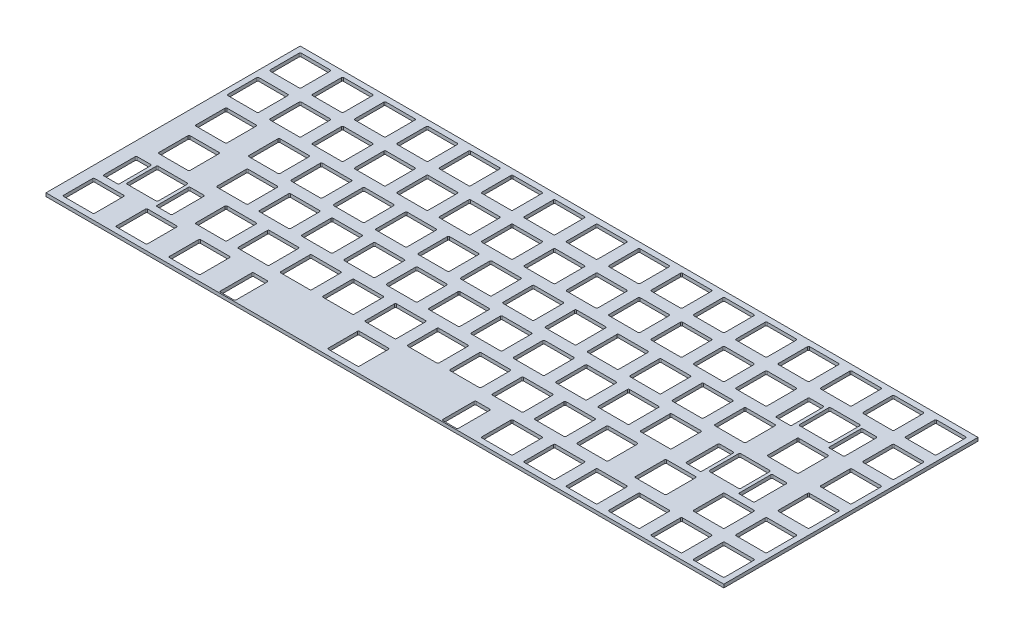
SolidWorks part; units mm, degrees
ref_plane "Front Plane" through (0, 0, 0) normal (0, 0, 1) x (1, 0, 0)
ref_plane "Top Plane" through (0, 0, 0) normal (0, 1, 0) x (1, 0, 0)
ref_plane "Right Plane" through (0, 0, 0) normal (1, 0, 0) x (0, 0, -1)
sketch "Sketch2" plane through (0, 0, 0) normal (0, 1, 0) x (1, 0, 0)
  line L0 (3.025, -2.525) -> (16.025, -2.525)
  line L1 (3.025, -16.525) -> (16.025, -16.525)
  line L2 (2.525, -3.025) -> (2.525, -16.025)
  line L3 (16.525, -3.025) -> (16.525, -16.025)
  line L4 (22.075, -2.525) -> (35.075, -2.525)
  line L5 (22.075, -16.525) -> (35.075, -16.525)
  line L6 (21.575, -3.025) -> (21.575, -16.025)
  line L7 (35.575, -3.025) -> (35.575, -16.025)
  line L8 (41.125, -2.525) -> (54.125, -2.525)
  line L9 (41.125, -16.525) -> (54.125, -16.525)
  line L10 (40.625, -3.025) -> (40.625, -16.025)
  line L11 (54.625, -3.025) -> (54.625, -16.025)
  line L12 (60.175, -2.525) -> (73.175, -2.525)
  line L13 (60.175, -16.525) -> (73.175, -16.525)
  line L14 (59.675, -3.025) -> (59.675, -16.025)
  line L15 (73.675, -3.025) -> (73.675, -16.025)
  line L16 (79.225, -2.525) -> (92.225, -2.525)
  line L17 (79.225, -16.525) -> (92.225, -16.525)
  line L18 (78.725, -3.025) -> (78.725, -16.025)
  line L19 (92.725, -3.025) -> (92.725, -16.025)
  line L20 (98.275, -2.525) -> (111.275, -2.525)
  line L21 (98.275, -16.525) -> (111.275, -16.525)
  line L22 (97.775, -3.025) -> (97.775, -16.025)
  line L23 (111.775, -3.025) -> (111.775, -16.025)
  line L24 (117.325, -2.525) -> (130.325, -2.525)
  line L25 (117.325, -16.525) -> (130.325, -16.525)
  line L26 (116.825, -3.025) -> (116.825, -16.025)
  line L27 (130.825, -3.025) -> (130.825, -16.025)
  line L28 (136.375, -2.525) -> (149.375, -2.525)
  line L29 (136.375, -16.525) -> (149.375, -16.525)
  line L30 (135.875, -3.025) -> (135.875, -16.025)
  line L31 (149.875, -3.025) -> (149.875, -16.025)
  line L32 (155.425, -2.525) -> (168.425, -2.525)
  line L33 (155.425, -16.525) -> (168.425, -16.525)
  line L34 (154.925, -3.025) -> (154.925, -16.025)
  line L35 (168.925, -3.025) -> (168.925, -16.025)
  line L36 (174.475, -2.525) -> (187.475, -2.525)
  line L37 (174.475, -16.525) -> (187.475, -16.525)
  line L38 (173.975, -3.025) -> (173.975, -16.025)
  line L39 (187.975, -3.025) -> (187.975, -16.025)
  line L40 (193.525, -2.525) -> (206.525, -2.525)
  line L41 (193.525, -16.525) -> (206.525, -16.525)
  line L42 (193.025, -3.025) -> (193.025, -16.025)
  line L43 (207.025, -3.025) -> (207.025, -16.025)
  line L44 (212.575, -2.525) -> (225.575, -2.525)
  line L45 (212.575, -16.525) -> (225.575, -16.525)
  line L46 (212.075, -3.025) -> (212.075, -16.025)
  line L47 (226.075, -3.025) -> (226.075, -16.025)
  line L48 (231.625, -2.525) -> (244.625, -2.525)
  line L49 (231.625, -16.525) -> (244.625, -16.525)
  line L50 (231.125, -3.025) -> (231.125, -16.025)
  line L51 (245.125, -3.025) -> (245.125, -16.025)
  line L52 (250.675, -2.525) -> (263.675, -2.525)
  line L53 (250.675, -16.525) -> (263.675, -16.525)
  line L54 (250.175, -3.025) -> (250.175, -16.025)
  line L55 (264.175, -3.025) -> (264.175, -16.025)
  line L56 (269.725, -2.525) -> (282.725, -2.525)
  line L57 (269.725, -16.525) -> (282.725, -16.525)
  line L58 (269.225, -3.025) -> (269.225, -16.025)
  line L59 (283.225, -3.025) -> (283.225, -16.025)
  line L60 (288.775, -2.525) -> (301.775, -2.525)
  line L61 (288.775, -16.525) -> (301.775, -16.525)
  line L62 (288.275, -3.025) -> (288.275, -16.025)
  line L63 (302.275, -3.025) -> (302.275, -16.025)
  line L64 (3.025, -21.575) -> (16.025, -21.575)
  line L65 (3.025, -35.575) -> (16.025, -35.575)
  line L66 (2.525, -22.075) -> (2.525, -35.075)
  line L67 (16.525, -22.075) -> (16.525, -35.075)
  line L68 (22.075, -21.575) -> (35.075, -21.575)
  line L69 (22.075, -35.575) -> (35.075, -35.575)
  line L70 (21.575, -22.075) -> (21.575, -35.075)
  line L71 (35.575, -22.075) -> (35.575, -35.075)
  line L72 (41.125, -21.575) -> (54.125, -21.575)
  line L73 (41.125, -35.575) -> (54.125, -35.575)
  line L74 (40.625, -22.075) -> (40.625, -35.075)
  line L75 (54.625, -22.075) -> (54.625, -35.075)
  line L76 (60.175, -21.575) -> (73.175, -21.575)
  line L77 (60.175, -35.575) -> (73.175, -35.575)
  line L78 (59.675, -22.075) -> (59.675, -35.075)
  line L79 (73.675, -22.075) -> (73.675, -35.075)
  line L80 (79.225, -21.575) -> (92.225, -21.575)
  line L81 (79.225, -35.575) -> (92.225, -35.575)
  line L82 (78.725, -22.075) -> (78.725, -35.075)
  line L83 (92.725, -22.075) -> (92.725, -35.075)
  line L84 (98.275, -21.575) -> (111.275, -21.575)
  line L85 (98.275, -35.575) -> (111.275, -35.575)
  line L86 (97.775, -22.075) -> (97.775, -35.075)
  line L87 (111.775, -22.075) -> (111.775, -35.075)
  line L88 (117.325, -21.575) -> (130.325, -21.575)
  line L89 (117.325, -35.575) -> (130.325, -35.575)
  line L90 (116.825, -22.075) -> (116.825, -35.075)
  line L91 (130.825, -22.075) -> (130.825, -35.075)
  line L92 (136.375, -21.575) -> (149.375, -21.575)
  line L93 (136.375, -35.575) -> (149.375, -35.575)
  line L94 (135.875, -22.075) -> (135.875, -35.075)
  line L95 (149.875, -22.075) -> (149.875, -35.075)
  line L96 (155.425, -21.575) -> (168.425, -21.575)
  line L97 (155.425, -35.575) -> (168.425, -35.575)
  line L98 (154.925, -22.075) -> (154.925, -35.075)
  line L99 (168.925, -22.075) -> (168.925, -35.075)
  line L100 (174.475, -21.575) -> (187.475, -21.575)
  line L101 (174.475, -35.575) -> (187.475, -35.575)
  line L102 (173.975, -22.075) -> (173.975, -35.075)
  line L103 (187.975, -22.075) -> (187.975, -35.075)
  line L104 (193.525, -21.575) -> (206.525, -21.575)
  line L105 (193.525, -35.575) -> (206.525, -35.575)
  line L106 (193.025, -22.075) -> (193.025, -35.075)
  line L107 (207.025, -22.075) -> (207.025, -35.075)
  line L108 (212.575, -21.575) -> (225.575, -21.575)
  line L109 (212.575, -35.575) -> (225.575, -35.575)
  line L110 (212.075, -22.075) -> (212.075, -35.075)
  line L111 (226.075, -22.075) -> (226.075, -35.075)
  line L112 (231.625, -21.575) -> (244.625, -21.575)
  line L113 (231.625, -35.575) -> (244.625, -35.575)
  line L114 (231.125, -22.075) -> (231.125, -35.075)
  line L115 (245.125, -22.075) -> (245.125, -35.075)
  line L116 (260.2, -21.575) -> (273.2, -21.575)
  line L117 (260.2, -35.575) -> (273.2, -35.575)
  line L118 (259.7, -22.075) -> (259.7, -35.075)
  line L119 (273.7, -22.075) -> (273.7, -35.075)
  line L120 (251.762, -22.575) -> (257.762, -22.575)
  line L121 (251.762, -37.575) -> (257.762, -37.575)
  line L122 (251.262, -23.075) -> (251.262, -37.075)
  line L123 (258.262, -23.075) -> (258.262, -37.075)
  line L124 (275.638, -22.575) -> (281.638, -22.575)
  line L125 (275.638, -37.575) -> (281.638, -37.575)
  line L126 (275.138, -23.075) -> (275.138, -37.075)
  line L127 (282.138, -23.075) -> (282.138, -37.075)
  line L128 (288.775, -21.575) -> (301.775, -21.575)
  line L129 (288.775, -35.575) -> (301.775, -35.575)
  line L130 (288.275, -22.075) -> (288.275, -35.075)
  line L131 (302.275, -22.075) -> (302.275, -35.075)
  line L132 (7.7875, -40.625) -> (20.7875, -40.625)
  line L133 (7.7875, -54.625) -> (20.7875, -54.625)
  line L134 (7.2875, -41.125) -> (7.2875, -54.125)
  line L135 (21.2875, -41.125) -> (21.2875, -54.125)
  line L136 (31.6, -40.625) -> (44.6, -40.625)
  line L137 (31.6, -54.625) -> (44.6, -54.625)
  line L138 (31.1, -41.125) -> (31.1, -54.125)
  line L139 (45.1, -41.125) -> (45.1, -54.125)
  line L140 (50.65, -40.625) -> (63.65, -40.625)
  line L141 (50.65, -54.625) -> (63.65, -54.625)
  line L142 (50.15, -41.125) -> (50.15, -54.125)
  line L143 (64.15, -41.125) -> (64.15, -54.125)
  line L144 (69.7, -40.625) -> (82.7, -40.625)
  line L145 (69.7, -54.625) -> (82.7, -54.625)
  line L146 (69.2, -41.125) -> (69.2, -54.125)
  line L147 (83.2, -41.125) -> (83.2, -54.125)
  line L148 (88.75, -40.625) -> (101.75, -40.625)
  line L149 (88.75, -54.625) -> (101.75, -54.625)
  line L150 (88.25, -41.125) -> (88.25, -54.125)
  line L151 (102.25, -41.125) -> (102.25, -54.125)
  line L152 (107.8, -40.625) -> (120.8, -40.625)
  line L153 (107.8, -54.625) -> (120.8, -54.625)
  line L154 (107.3, -41.125) -> (107.3, -54.125)
  line L155 (121.3, -41.125) -> (121.3, -54.125)
  line L156 (126.85, -40.625) -> (139.85, -40.625)
  line L157 (126.85, -54.625) -> (139.85, -54.625)
  line L158 (126.35, -41.125) -> (126.35, -54.125)
  line L159 (140.35, -41.125) -> (140.35, -54.125)
  line L160 (145.9, -40.625) -> (158.9, -40.625)
  line L161 (145.9, -54.625) -> (158.9, -54.625)
  line L162 (145.4, -41.125) -> (145.4, -54.125)
  line L163 (159.4, -41.125) -> (159.4, -54.125)
  line L164 (164.95, -40.625) -> (177.95, -40.625)
  line L165 (164.95, -54.625) -> (177.95, -54.625)
  line L166 (164.45, -41.125) -> (164.45, -54.125)
  line L167 (178.45, -41.125) -> (178.45, -54.125)
  line L168 (184, -40.625) -> (197, -40.625)
  line L169 (184, -54.625) -> (197, -54.625)
  line L170 (183.5, -41.125) -> (183.5, -54.125)
  line L171 (197.5, -41.125) -> (197.5, -54.125)
  line L172 (203.05, -40.625) -> (216.05, -40.625)
  line L173 (203.05, -54.625) -> (216.05, -54.625)
  line L174 (202.55, -41.125) -> (202.55, -54.125)
  line L175 (216.55, -41.125) -> (216.55, -54.125)
  line L176 (222.1, -40.625) -> (235.1, -40.625)
  line L177 (222.1, -54.625) -> (235.1, -54.625)
  line L178 (221.6, -41.125) -> (221.6, -54.125)
  line L179 (235.6, -41.125) -> (235.6, -54.125)
  line L180 (241.15, -40.625) -> (254.15, -40.625)
  line L181 (241.15, -54.625) -> (254.15, -54.625)
  line L182 (240.65, -41.125) -> (240.65, -54.125)
  line L183 (254.65, -41.125) -> (254.65, -54.125)
  line L184 (264.9625, -40.625) -> (277.9625, -40.625)
  line L185 (264.9625, -54.625) -> (277.9625, -54.625)
  line L186 (264.4625, -41.125) -> (264.4625, -54.125)
  line L187 (278.4625, -41.125) -> (278.4625, -54.125)
  line L188 (288.775, -40.625) -> (301.775, -40.625)
  line L189 (288.775, -54.625) -> (301.775, -54.625)
  line L190 (288.275, -41.125) -> (288.275, -54.125)
  line L191 (302.275, -41.125) -> (302.275, -54.125)
  line L192 (10.1687, -59.675) -> (23.1687, -59.675)
  line L193 (10.1687, -73.675) -> (23.1687, -73.675)
  line L194 (9.6688, -60.175) -> (9.6688, -73.175)
  line L195 (23.6687, -60.175) -> (23.6687, -73.175)
  line L196 (36.3625, -59.675) -> (49.3625, -59.675)
  line L197 (36.3625, -73.675) -> (49.3625, -73.675)
  line L198 (35.8625, -60.175) -> (35.8625, -73.175)
  line L199 (49.8625, -60.175) -> (49.8625, -73.175)
  line L200 (55.4125, -59.675) -> (68.4125, -59.675)
  line L201 (55.4125, -73.675) -> (68.4125, -73.675)
  line L202 (54.9125, -60.175) -> (54.9125, -73.175)
  line L203 (68.9125, -60.175) -> (68.9125, -73.175)
  line L204 (74.4625, -59.675) -> (87.4625, -59.675)
  line L205 (74.4625, -73.675) -> (87.4625, -73.675)
  line L206 (73.9625, -60.175) -> (73.9625, -73.175)
  line L207 (87.9625, -60.175) -> (87.9625, -73.175)
  line L208 (93.5125, -59.675) -> (106.5125, -59.675)
  line L209 (93.5125, -73.675) -> (106.5125, -73.675)
  line L210 (93.0125, -60.175) -> (93.0125, -73.175)
  line L211 (107.0125, -60.175) -> (107.0125, -73.175)
  line L212 (112.5625, -59.675) -> (125.5625, -59.675)
  line L213 (112.5625, -73.675) -> (125.5625, -73.675)
  line L214 (112.0625, -60.175) -> (112.0625, -73.175)
  line L215 (126.0625, -60.175) -> (126.0625, -73.175)
  line L216 (131.6125, -59.675) -> (144.6125, -59.675)
  line L217 (131.6125, -73.675) -> (144.6125, -73.675)
  line L218 (131.1125, -60.175) -> (131.1125, -73.175)
  line L219 (145.1125, -60.175) -> (145.1125, -73.175)
  line L220 (150.6625, -59.675) -> (163.6625, -59.675)
  line L221 (150.6625, -73.675) -> (163.6625, -73.675)
  line L222 (150.1625, -60.175) -> (150.1625, -73.175)
  line L223 (164.1625, -60.175) -> (164.1625, -73.175)
  line L224 (169.7125, -59.675) -> (182.7125, -59.675)
  line L225 (169.7125, -73.675) -> (182.7125, -73.675)
  line L226 (169.2125, -60.175) -> (169.2125, -73.175)
  line L227 (183.2125, -60.175) -> (183.2125, -73.175)
  line L228 (188.7625, -59.675) -> (201.7625, -59.675)
  line L229 (188.7625, -73.675) -> (201.7625, -73.675)
  line L230 (188.2625, -60.175) -> (188.2625, -73.175)
  line L231 (202.2625, -60.175) -> (202.2625, -73.175)
  line L232 (207.8125, -59.675) -> (220.8125, -59.675)
  line L233 (207.8125, -73.675) -> (220.8125, -73.675)
  line L234 (207.3125, -60.175) -> (207.3125, -73.175)
  line L235 (221.3125, -60.175) -> (221.3125, -73.175)
  line L236 (226.8625, -59.675) -> (239.8625, -59.675)
  line L237 (226.8625, -73.675) -> (239.8625, -73.675)
  line L238 (226.3625, -60.175) -> (226.3625, -73.175)
  line L239 (240.3625, -60.175) -> (240.3625, -73.175)
  line L240 (257.8188, -59.675) -> (270.8188, -59.675)
  line L241 (257.8188, -73.675) -> (270.8188, -73.675)
  line L242 (257.3188, -60.175) -> (257.3188, -73.175)
  line L243 (271.3188, -60.175) -> (271.3188, -73.175)
  line L244 (249.3808, -60.675) -> (255.3807, -60.675)
  line L245 (249.3808, -75.675) -> (255.3807, -75.675)
  line L246 (248.8808, -61.175) -> (248.8808, -75.175)
  line L247 (255.8807, -61.175) -> (255.8807, -75.175)
  line L248 (273.2568, -60.675) -> (279.2568, -60.675)
  line L249 (273.2568, -75.675) -> (279.2568, -75.675)
  line L250 (272.7568, -61.175) -> (272.7568, -75.175)
  line L251 (279.7568, -61.175) -> (279.7568, -75.175)
  line L252 (288.775, -59.675) -> (301.775, -59.675)
  line L253 (288.775, -73.675) -> (301.775, -73.675)
  line L254 (288.275, -60.175) -> (288.275, -73.175)
  line L255 (302.275, -60.175) -> (302.275, -73.175)
  line L256 (14.9313, -78.725) -> (27.9312, -78.725)
  line L257 (14.9313, -92.725) -> (27.9312, -92.725)
  line L258 (14.4313, -79.225) -> (14.4313, -92.225)
  line L259 (28.4312, -79.225) -> (28.4312, -92.225)
  line L260 (6.4932, -79.725) -> (12.4932, -79.725)
  line L261 (6.4932, -94.725) -> (12.4932, -94.725)
  line L262 (5.9932, -80.225) -> (5.9932, -94.225)
  line L263 (12.9932, -80.225) -> (12.9932, -94.225)
  line L264 (30.3693, -79.725) -> (36.3693, -79.725)
  line L265 (30.3693, -94.725) -> (36.3693, -94.725)
  line L266 (29.8693, -80.225) -> (29.8693, -94.225)
  line L267 (36.8693, -80.225) -> (36.8693, -94.225)
  line L268 (45.8875, -78.725) -> (58.8875, -78.725)
  line L269 (45.8875, -92.725) -> (58.8875, -92.725)
  line L270 (45.3875, -79.225) -> (45.3875, -92.225)
  line L271 (59.3875, -79.225) -> (59.3875, -92.225)
  line L272 (64.9375, -78.725) -> (77.9375, -78.725)
  line L273 (64.9375, -92.725) -> (77.9375, -92.725)
  line L274 (64.4375, -79.225) -> (64.4375, -92.225)
  line L275 (78.4375, -79.225) -> (78.4375, -92.225)
  line L276 (83.9875, -78.725) -> (96.9875, -78.725)
  line L277 (83.9875, -92.725) -> (96.9875, -92.725)
  line L278 (83.4875, -79.225) -> (83.4875, -92.225)
  line L279 (97.4875, -79.225) -> (97.4875, -92.225)
  line L280 (103.0375, -78.725) -> (116.0375, -78.725)
  line L281 (103.0375, -92.725) -> (116.0375, -92.725)
  line L282 (102.5375, -79.225) -> (102.5375, -92.225)
  line L283 (116.5375, -79.225) -> (116.5375, -92.225)
  line L284 (122.0875, -78.725) -> (135.0875, -78.725)
  line L285 (122.0875, -92.725) -> (135.0875, -92.725)
  line L286 (121.5875, -79.225) -> (121.5875, -92.225)
  line L287 (135.5875, -79.225) -> (135.5875, -92.225)
  line L288 (141.1375, -78.725) -> (154.1375, -78.725)
  line L289 (141.1375, -92.725) -> (154.1375, -92.725)
  line L290 (140.6375, -79.225) -> (140.6375, -92.225)
  line L291 (154.6375, -79.225) -> (154.6375, -92.225)
  line L292 (160.1875, -78.725) -> (173.1875, -78.725)
  line L293 (160.1875, -92.725) -> (173.1875, -92.725)
  line L294 (159.6875, -79.225) -> (159.6875, -92.225)
  line L295 (173.6875, -79.225) -> (173.6875, -92.225)
  line L296 (179.2375, -78.725) -> (192.2375, -78.725)
  line L297 (179.2375, -92.725) -> (192.2375, -92.725)
  line L298 (178.7375, -79.225) -> (178.7375, -92.225)
  line L299 (192.7375, -79.225) -> (192.7375, -92.225)
  line L300 (198.2875, -78.725) -> (211.2875, -78.725)
  line L301 (198.2875, -92.725) -> (211.2875, -92.725)
  line L302 (197.7875, -79.225) -> (197.7875, -92.225)
  line L303 (211.7875, -79.225) -> (211.7875, -92.225)
  line L304 (217.3375, -78.725) -> (230.3375, -78.725)
  line L305 (217.3375, -92.725) -> (230.3375, -92.725)
  line L306 (216.8375, -79.225) -> (216.8375, -92.225)
  line L307 (230.8375, -79.225) -> (230.8375, -92.225)
  line L308 (243.5312, -78.725) -> (256.5312, -78.725)
  line L309 (243.5312, -92.725) -> (256.5312, -92.725)
  line L310 (243.0312, -79.225) -> (243.0312, -92.225)
  line L311 (257.0312, -79.225) -> (257.0312, -92.225)
  line L312 (269.725, -78.725) -> (282.725, -78.725)
  line L313 (269.725, -92.725) -> (282.725, -92.725)
  line L314 (269.225, -79.225) -> (269.225, -92.225)
  line L315 (283.225, -79.225) -> (283.225, -92.225)
  line L316 (288.775, -78.725) -> (301.775, -78.725)
  line L317 (288.775, -92.725) -> (301.775, -92.725)
  line L318 (288.275, -79.225) -> (288.275, -92.225)
  line L319 (302.275, -79.225) -> (302.275, -92.225)
  line L320 (5.4063, -97.775) -> (18.4062, -97.775)
  line L321 (5.4063, -111.775) -> (18.4062, -111.775)
  line L322 (4.9062, -98.275) -> (4.9062, -111.275)
  line L323 (18.9062, -98.275) -> (18.9062, -111.275)
  line L324 (29.2188, -97.775) -> (42.2188, -97.775)
  line L325 (29.2188, -111.775) -> (42.2188, -111.775)
  line L326 (28.7188, -98.275) -> (28.7188, -111.275)
  line L327 (42.7188, -98.275) -> (42.7188, -111.275)
  line L328 (53.0312, -97.775) -> (66.0312, -97.775)
  line L329 (53.0312, -111.775) -> (66.0312, -111.775)
  line L330 (52.5312, -98.275) -> (52.5312, -111.275)
  line L331 (66.5312, -98.275) -> (66.5312, -111.275)
  line L332 (124.4688, -97.775) -> (137.4688, -97.775)
  line L333 (124.4688, -111.775) -> (137.4688, -111.775)
  line L334 (123.9688, -98.275) -> (123.9688, -111.275)
  line L335 (137.9688, -98.275) -> (137.9688, -111.275)
  line L336 (77.9688, -98.775) -> (83.9688, -98.775)
  line L337 (77.9688, -113.775) -> (83.9688, -113.775)
  line L338 (77.4688, -99.275) -> (77.4688, -113.275)
  line L339 (84.4688, -99.275) -> (84.4688, -113.275)
  line L340 (177.9688, -98.775) -> (183.9688, -98.775)
  line L341 (177.9688, -113.775) -> (183.9688, -113.775)
  line L342 (177.4688, -99.275) -> (177.4688, -113.275)
  line L343 (184.4688, -99.275) -> (184.4688, -113.275)
  line L344 (193.525, -97.775) -> (206.525, -97.775)
  line L345 (193.525, -111.775) -> (206.525, -111.775)
  line L346 (193.025, -98.275) -> (193.025, -111.275)
  line L347 (207.025, -98.275) -> (207.025, -111.275)
  line L348 (212.575, -97.775) -> (225.575, -97.775)
  line L349 (212.575, -111.775) -> (225.575, -111.775)
  line L350 (212.075, -98.275) -> (212.075, -111.275)
  line L351 (226.075, -98.275) -> (226.075, -111.275)
  line L352 (231.625, -97.775) -> (244.625, -97.775)
  line L353 (231.625, -111.775) -> (244.625, -111.775)
  line L354 (231.125, -98.275) -> (231.125, -111.275)
  line L355 (245.125, -98.275) -> (245.125, -111.275)
  line L356 (250.675, -97.775) -> (263.675, -97.775)
  line L357 (250.675, -111.775) -> (263.675, -111.775)
  line L358 (250.175, -98.275) -> (250.175, -111.275)
  line L359 (264.175, -98.275) -> (264.175, -111.275)
  line L360 (269.725, -97.775) -> (282.725, -97.775)
  line L361 (269.725, -111.775) -> (282.725, -111.775)
  line L362 (269.225, -98.275) -> (269.225, -111.275)
  line L363 (283.225, -98.275) -> (283.225, -111.275)
  line L364 (288.775, -97.775) -> (301.775, -97.775)
  line L365 (288.775, -111.775) -> (301.775, -111.775)
  line L366 (288.275, -98.275) -> (288.275, -111.275)
  line L367 (302.275, -98.275) -> (302.275, -111.275)
  line L368 (0, -114.3) -> (304.8, -114.3)
  line L369 (0, 0) -> (304.8, 0)
  line L370 (0, -114.3) -> (0, 0)
  line L371 (304.8, -114.3) -> (304.8, 0)
  arc A0 (3.025, -2.525) -> (2.525, -3.025) centre (3.025, -3.025) ccw
  arc A1 (16.525, -3.025) -> (16.025, -2.525) centre (16.025, -3.025) ccw
  arc A2 (2.525, -16.025) -> (3.025, -16.525) centre (3.025, -16.025) ccw
  arc A3 (16.025, -16.525) -> (16.525, -16.025) centre (16.025, -16.025) ccw
  arc A4 (22.075, -2.525) -> (21.575, -3.025) centre (22.075, -3.025) ccw
  arc A5 (35.575, -3.025) -> (35.075, -2.525) centre (35.075, -3.025) ccw
  arc A6 (21.575, -16.025) -> (22.075, -16.525) centre (22.075, -16.025) ccw
  arc A7 (35.075, -16.525) -> (35.575, -16.025) centre (35.075, -16.025) ccw
  arc A8 (41.125, -2.525) -> (40.625, -3.025) centre (41.125, -3.025) ccw
  arc A9 (54.625, -3.025) -> (54.125, -2.525) centre (54.125, -3.025) ccw
  arc A10 (40.625, -16.025) -> (41.125, -16.525) centre (41.125, -16.025) ccw
  arc A11 (54.125, -16.525) -> (54.625, -16.025) centre (54.125, -16.025) ccw
  arc A12 (60.175, -2.525) -> (59.675, -3.025) centre (60.175, -3.025) ccw
  arc A13 (73.675, -3.025) -> (73.175, -2.525) centre (73.175, -3.025) ccw
  arc A14 (59.675, -16.025) -> (60.175, -16.525) centre (60.175, -16.025) ccw
  arc A15 (73.175, -16.525) -> (73.675, -16.025) centre (73.175, -16.025) ccw
  arc A16 (79.225, -2.525) -> (78.725, -3.025) centre (79.225, -3.025) ccw
  arc A17 (92.725, -3.025) -> (92.225, -2.525) centre (92.225, -3.025) ccw
  arc A18 (78.725, -16.025) -> (79.225, -16.525) centre (79.225, -16.025) ccw
  arc A19 (92.225, -16.525) -> (92.725, -16.025) centre (92.225, -16.025) ccw
  arc A20 (98.275, -2.525) -> (97.775, -3.025) centre (98.275, -3.025) ccw
  arc A21 (111.775, -3.025) -> (111.275, -2.525) centre (111.275, -3.025) ccw
  arc A22 (97.775, -16.025) -> (98.275, -16.525) centre (98.275, -16.025) ccw
  arc A23 (111.275, -16.525) -> (111.775, -16.025) centre (111.275, -16.025) ccw
  arc A24 (117.325, -2.525) -> (116.825, -3.025) centre (117.325, -3.025) ccw
  arc A25 (130.825, -3.025) -> (130.325, -2.525) centre (130.325, -3.025) ccw
  arc A26 (116.825, -16.025) -> (117.325, -16.525) centre (117.325, -16.025) ccw
  arc A27 (130.325, -16.525) -> (130.825, -16.025) centre (130.325, -16.025) ccw
  arc A28 (136.375, -2.525) -> (135.875, -3.025) centre (136.375, -3.025) ccw
  arc A29 (149.875, -3.025) -> (149.375, -2.525) centre (149.375, -3.025) ccw
  arc A30 (135.875, -16.025) -> (136.375, -16.525) centre (136.375, -16.025) ccw
  arc A31 (149.375, -16.525) -> (149.875, -16.025) centre (149.375, -16.025) ccw
  arc A32 (155.425, -2.525) -> (154.925, -3.025) centre (155.425, -3.025) ccw
  arc A33 (168.925, -3.025) -> (168.425, -2.525) centre (168.425, -3.025) ccw
  arc A34 (154.925, -16.025) -> (155.425, -16.525) centre (155.425, -16.025) ccw
  arc A35 (168.425, -16.525) -> (168.925, -16.025) centre (168.425, -16.025) ccw
  arc A36 (174.475, -2.525) -> (173.975, -3.025) centre (174.475, -3.025) ccw
  arc A37 (187.975, -3.025) -> (187.475, -2.525) centre (187.475, -3.025) ccw
  arc A38 (173.975, -16.025) -> (174.475, -16.525) centre (174.475, -16.025) ccw
  arc A39 (187.475, -16.525) -> (187.975, -16.025) centre (187.475, -16.025) ccw
  arc A40 (193.525, -2.525) -> (193.025, -3.025) centre (193.525, -3.025) ccw
  arc A41 (207.025, -3.025) -> (206.525, -2.525) centre (206.525, -3.025) ccw
  arc A42 (193.025, -16.025) -> (193.525, -16.525) centre (193.525, -16.025) ccw
  arc A43 (206.525, -16.525) -> (207.025, -16.025) centre (206.525, -16.025) ccw
  arc A44 (212.575, -2.525) -> (212.075, -3.025) centre (212.575, -3.025) ccw
  arc A45 (226.075, -3.025) -> (225.575, -2.525) centre (225.575, -3.025) ccw
  arc A46 (212.075, -16.025) -> (212.575, -16.525) centre (212.575, -16.025) ccw
  arc A47 (225.575, -16.525) -> (226.075, -16.025) centre (225.575, -16.025) ccw
  arc A48 (231.625, -2.525) -> (231.125, -3.025) centre (231.625, -3.025) ccw
  arc A49 (245.125, -3.025) -> (244.625, -2.525) centre (244.625, -3.025) ccw
  arc A50 (231.125, -16.025) -> (231.625, -16.525) centre (231.625, -16.025) ccw
  arc A51 (244.625, -16.525) -> (245.125, -16.025) centre (244.625, -16.025) ccw
  arc A52 (250.675, -2.525) -> (250.175, -3.025) centre (250.675, -3.025) ccw
  arc A53 (264.175, -3.025) -> (263.675, -2.525) centre (263.675, -3.025) ccw
  arc A54 (250.175, -16.025) -> (250.675, -16.525) centre (250.675, -16.025) ccw
  arc A55 (263.675, -16.525) -> (264.175, -16.025) centre (263.675, -16.025) ccw
  arc A56 (269.725, -2.525) -> (269.225, -3.025) centre (269.725, -3.025) ccw
  arc A57 (283.225, -3.025) -> (282.725, -2.525) centre (282.725, -3.025) ccw
  arc A58 (269.225, -16.025) -> (269.725, -16.525) centre (269.725, -16.025) ccw
  arc A59 (282.725, -16.525) -> (283.225, -16.025) centre (282.725, -16.025) ccw
  arc A60 (288.775, -2.525) -> (288.275, -3.025) centre (288.775, -3.025) ccw
  arc A61 (302.275, -3.025) -> (301.775, -2.525) centre (301.775, -3.025) ccw
  arc A62 (288.275, -16.025) -> (288.775, -16.525) centre (288.775, -16.025) ccw
  arc A63 (301.775, -16.525) -> (302.275, -16.025) centre (301.775, -16.025) ccw
  arc A64 (3.025, -21.575) -> (2.525, -22.075) centre (3.025, -22.075) ccw
  arc A65 (16.525, -22.075) -> (16.025, -21.575) centre (16.025, -22.075) ccw
  arc A66 (2.525, -35.075) -> (3.025, -35.575) centre (3.025, -35.075) ccw
  arc A67 (16.025, -35.575) -> (16.525, -35.075) centre (16.025, -35.075) ccw
  arc A68 (22.075, -21.575) -> (21.575, -22.075) centre (22.075, -22.075) ccw
  arc A69 (35.575, -22.075) -> (35.075, -21.575) centre (35.075, -22.075) ccw
  arc A70 (21.575, -35.075) -> (22.075, -35.575) centre (22.075, -35.075) ccw
  arc A71 (35.075, -35.575) -> (35.575, -35.075) centre (35.075, -35.075) ccw
  arc A72 (41.125, -21.575) -> (40.625, -22.075) centre (41.125, -22.075) ccw
  arc A73 (54.625, -22.075) -> (54.125, -21.575) centre (54.125, -22.075) ccw
  arc A74 (40.625, -35.075) -> (41.125, -35.575) centre (41.125, -35.075) ccw
  arc A75 (54.125, -35.575) -> (54.625, -35.075) centre (54.125, -35.075) ccw
  arc A76 (60.175, -21.575) -> (59.675, -22.075) centre (60.175, -22.075) ccw
  arc A77 (73.675, -22.075) -> (73.175, -21.575) centre (73.175, -22.075) ccw
  arc A78 (59.675, -35.075) -> (60.175, -35.575) centre (60.175, -35.075) ccw
  arc A79 (73.175, -35.575) -> (73.675, -35.075) centre (73.175, -35.075) ccw
  arc A80 (79.225, -21.575) -> (78.725, -22.075) centre (79.225, -22.075) ccw
  arc A81 (92.725, -22.075) -> (92.225, -21.575) centre (92.225, -22.075) ccw
  arc A82 (78.725, -35.075) -> (79.225, -35.575) centre (79.225, -35.075) ccw
  arc A83 (92.225, -35.575) -> (92.725, -35.075) centre (92.225, -35.075) ccw
  arc A84 (98.275, -21.575) -> (97.775, -22.075) centre (98.275, -22.075) ccw
  arc A85 (111.775, -22.075) -> (111.275, -21.575) centre (111.275, -22.075) ccw
  arc A86 (97.775, -35.075) -> (98.275, -35.575) centre (98.275, -35.075) ccw
  arc A87 (111.275, -35.575) -> (111.775, -35.075) centre (111.275, -35.075) ccw
  arc A88 (117.325, -21.575) -> (116.825, -22.075) centre (117.325, -22.075) ccw
  arc A89 (130.825, -22.075) -> (130.325, -21.575) centre (130.325, -22.075) ccw
  arc A90 (116.825, -35.075) -> (117.325, -35.575) centre (117.325, -35.075) ccw
  arc A91 (130.325, -35.575) -> (130.825, -35.075) centre (130.325, -35.075) ccw
  arc A92 (136.375, -21.575) -> (135.875, -22.075) centre (136.375, -22.075) ccw
  arc A93 (149.875, -22.075) -> (149.375, -21.575) centre (149.375, -22.075) ccw
  arc A94 (135.875, -35.075) -> (136.375, -35.575) centre (136.375, -35.075) ccw
  arc A95 (149.375, -35.575) -> (149.875, -35.075) centre (149.375, -35.075) ccw
  arc A96 (155.425, -21.575) -> (154.925, -22.075) centre (155.425, -22.075) ccw
  arc A97 (168.925, -22.075) -> (168.425, -21.575) centre (168.425, -22.075) ccw
  arc A98 (154.925, -35.075) -> (155.425, -35.575) centre (155.425, -35.075) ccw
  arc A99 (168.425, -35.575) -> (168.925, -35.075) centre (168.425, -35.075) ccw
  arc A100 (174.475, -21.575) -> (173.975, -22.075) centre (174.475, -22.075) ccw
  arc A101 (187.975, -22.075) -> (187.475, -21.575) centre (187.475, -22.075) ccw
  arc A102 (173.975, -35.075) -> (174.475, -35.575) centre (174.475, -35.075) ccw
  arc A103 (187.475, -35.575) -> (187.975, -35.075) centre (187.475, -35.075) ccw
  arc A104 (193.525, -21.575) -> (193.025, -22.075) centre (193.525, -22.075) ccw
  arc A105 (207.025, -22.075) -> (206.525, -21.575) centre (206.525, -22.075) ccw
  arc A106 (193.025, -35.075) -> (193.525, -35.575) centre (193.525, -35.075) ccw
  arc A107 (206.525, -35.575) -> (207.025, -35.075) centre (206.525, -35.075) ccw
  arc A108 (212.575, -21.575) -> (212.075, -22.075) centre (212.575, -22.075) ccw
  arc A109 (226.075, -22.075) -> (225.575, -21.575) centre (225.575, -22.075) ccw
  arc A110 (212.075, -35.075) -> (212.575, -35.575) centre (212.575, -35.075) ccw
  arc A111 (225.575, -35.575) -> (226.075, -35.075) centre (225.575, -35.075) ccw
  arc A112 (231.625, -21.575) -> (231.125, -22.075) centre (231.625, -22.075) ccw
  arc A113 (245.125, -22.075) -> (244.625, -21.575) centre (244.625, -22.075) ccw
  arc A114 (231.125, -35.075) -> (231.625, -35.575) centre (231.625, -35.075) ccw
  arc A115 (244.625, -35.575) -> (245.125, -35.075) centre (244.625, -35.075) ccw
  arc A116 (260.2, -21.575) -> (259.7, -22.075) centre (260.2, -22.075) ccw
  arc A117 (273.7, -22.075) -> (273.2, -21.575) centre (273.2, -22.075) ccw
  arc A118 (259.7, -35.075) -> (260.2, -35.575) centre (260.2, -35.075) ccw
  arc A119 (273.2, -35.575) -> (273.7, -35.075) centre (273.2, -35.075) ccw
  arc A120 (251.762, -22.575) -> (251.262, -23.075) centre (251.762, -23.075) ccw
  arc A121 (258.262, -23.075) -> (257.762, -22.575) centre (257.762, -23.075) ccw
  arc A122 (251.262, -37.075) -> (251.762, -37.575) centre (251.762, -37.075) ccw
  arc A123 (257.762, -37.575) -> (258.262, -37.075) centre (257.762, -37.075) ccw
  arc A124 (275.638, -22.575) -> (275.138, -23.075) centre (275.638, -23.075) ccw
  arc A125 (282.138, -23.075) -> (281.638, -22.575) centre (281.638, -23.075) ccw
  arc A126 (275.138, -37.075) -> (275.638, -37.575) centre (275.638, -37.075) ccw
  arc A127 (281.638, -37.575) -> (282.138, -37.075) centre (281.638, -37.075) ccw
  arc A128 (288.775, -21.575) -> (288.275, -22.075) centre (288.775, -22.075) ccw
  arc A129 (302.275, -22.075) -> (301.775, -21.575) centre (301.775, -22.075) ccw
  arc A130 (288.275, -35.075) -> (288.775, -35.575) centre (288.775, -35.075) ccw
  arc A131 (301.775, -35.575) -> (302.275, -35.075) centre (301.775, -35.075) ccw
  arc A132 (7.7875, -40.625) -> (7.2875, -41.125) centre (7.7875, -41.125) ccw
  arc A133 (21.2875, -41.125) -> (20.7875, -40.625) centre (20.7875, -41.125) ccw
  arc A134 (7.2875, -54.125) -> (7.7875, -54.625) centre (7.7875, -54.125) ccw
  arc A135 (20.7875, -54.625) -> (21.2875, -54.125) centre (20.7875, -54.125) ccw
  arc A136 (31.6, -40.625) -> (31.1, -41.125) centre (31.6, -41.125) ccw
  arc A137 (45.1, -41.125) -> (44.6, -40.625) centre (44.6, -41.125) ccw
  arc A138 (31.1, -54.125) -> (31.6, -54.625) centre (31.6, -54.125) ccw
  arc A139 (44.6, -54.625) -> (45.1, -54.125) centre (44.6, -54.125) ccw
  arc A140 (50.65, -40.625) -> (50.15, -41.125) centre (50.65, -41.125) ccw
  arc A141 (64.15, -41.125) -> (63.65, -40.625) centre (63.65, -41.125) ccw
  arc A142 (50.15, -54.125) -> (50.65, -54.625) centre (50.65, -54.125) ccw
  arc A143 (63.65, -54.625) -> (64.15, -54.125) centre (63.65, -54.125) ccw
  arc A144 (69.7, -40.625) -> (69.2, -41.125) centre (69.7, -41.125) ccw
  arc A145 (83.2, -41.125) -> (82.7, -40.625) centre (82.7, -41.125) ccw
  arc A146 (69.2, -54.125) -> (69.7, -54.625) centre (69.7, -54.125) ccw
  arc A147 (82.7, -54.625) -> (83.2, -54.125) centre (82.7, -54.125) ccw
  arc A148 (88.75, -40.625) -> (88.25, -41.125) centre (88.75, -41.125) ccw
  arc A149 (102.25, -41.125) -> (101.75, -40.625) centre (101.75, -41.125) ccw
  arc A150 (88.25, -54.125) -> (88.75, -54.625) centre (88.75, -54.125) ccw
  arc A151 (101.75, -54.625) -> (102.25, -54.125) centre (101.75, -54.125) ccw
  arc A152 (107.8, -40.625) -> (107.3, -41.125) centre (107.8, -41.125) ccw
  arc A153 (121.3, -41.125) -> (120.8, -40.625) centre (120.8, -41.125) ccw
  arc A154 (107.3, -54.125) -> (107.8, -54.625) centre (107.8, -54.125) ccw
  arc A155 (120.8, -54.625) -> (121.3, -54.125) centre (120.8, -54.125) ccw
  arc A156 (126.85, -40.625) -> (126.35, -41.125) centre (126.85, -41.125) ccw
  arc A157 (140.35, -41.125) -> (139.85, -40.625) centre (139.85, -41.125) ccw
  arc A158 (126.35, -54.125) -> (126.85, -54.625) centre (126.85, -54.125) ccw
  arc A159 (139.85, -54.625) -> (140.35, -54.125) centre (139.85, -54.125) ccw
  arc A160 (145.9, -40.625) -> (145.4, -41.125) centre (145.9, -41.125) ccw
  arc A161 (159.4, -41.125) -> (158.9, -40.625) centre (158.9, -41.125) ccw
  arc A162 (145.4, -54.125) -> (145.9, -54.625) centre (145.9, -54.125) ccw
  arc A163 (158.9, -54.625) -> (159.4, -54.125) centre (158.9, -54.125) ccw
  arc A164 (164.95, -40.625) -> (164.45, -41.125) centre (164.95, -41.125) ccw
  arc A165 (178.45, -41.125) -> (177.95, -40.625) centre (177.95, -41.125) ccw
  arc A166 (164.45, -54.125) -> (164.95, -54.625) centre (164.95, -54.125) ccw
  arc A167 (177.95, -54.625) -> (178.45, -54.125) centre (177.95, -54.125) ccw
  arc A168 (184, -40.625) -> (183.5, -41.125) centre (184, -41.125) ccw
  arc A169 (197.5, -41.125) -> (197, -40.625) centre (197, -41.125) ccw
  arc A170 (183.5, -54.125) -> (184, -54.625) centre (184, -54.125) ccw
  arc A171 (197, -54.625) -> (197.5, -54.125) centre (197, -54.125) ccw
  arc A172 (203.05, -40.625) -> (202.55, -41.125) centre (203.05, -41.125) ccw
  arc A173 (216.55, -41.125) -> (216.05, -40.625) centre (216.05, -41.125) ccw
  arc A174 (202.55, -54.125) -> (203.05, -54.625) centre (203.05, -54.125) ccw
  arc A175 (216.05, -54.625) -> (216.55, -54.125) centre (216.05, -54.125) ccw
  arc A176 (222.1, -40.625) -> (221.6, -41.125) centre (222.1, -41.125) ccw
  arc A177 (235.6, -41.125) -> (235.1, -40.625) centre (235.1, -41.125) ccw
  arc A178 (221.6, -54.125) -> (222.1, -54.625) centre (222.1, -54.125) ccw
  arc A179 (235.1, -54.625) -> (235.6, -54.125) centre (235.1, -54.125) ccw
  arc A180 (241.15, -40.625) -> (240.65, -41.125) centre (241.15, -41.125) ccw
  arc A181 (254.65, -41.125) -> (254.15, -40.625) centre (254.15, -41.125) ccw
  arc A182 (240.65, -54.125) -> (241.15, -54.625) centre (241.15, -54.125) ccw
  arc A183 (254.15, -54.625) -> (254.65, -54.125) centre (254.15, -54.125) ccw
  arc A184 (264.9625, -40.625) -> (264.4625, -41.125) centre (264.9625, -41.125) ccw
  arc A185 (278.4625, -41.125) -> (277.9625, -40.625) centre (277.9625, -41.125) ccw
  arc A186 (264.4625, -54.125) -> (264.9625, -54.625) centre (264.9625, -54.125) ccw
  arc A187 (277.9625, -54.625) -> (278.4625, -54.125) centre (277.9625, -54.125) ccw
  arc A188 (288.775, -40.625) -> (288.275, -41.125) centre (288.775, -41.125) ccw
  arc A189 (302.275, -41.125) -> (301.775, -40.625) centre (301.775, -41.125) ccw
  arc A190 (288.275, -54.125) -> (288.775, -54.625) centre (288.775, -54.125) ccw
  arc A191 (301.775, -54.625) -> (302.275, -54.125) centre (301.775, -54.125) ccw
  arc A192 (10.1687, -59.675) -> (9.6688, -60.175) centre (10.1687, -60.175) ccw
  arc A193 (23.6687, -60.175) -> (23.1687, -59.675) centre (23.1687, -60.175) ccw
  arc A194 (9.6688, -73.175) -> (10.1687, -73.675) centre (10.1687, -73.175) ccw
  arc A195 (23.1687, -73.675) -> (23.6687, -73.175) centre (23.1687, -73.175) ccw
  arc A196 (36.3625, -59.675) -> (35.8625, -60.175) centre (36.3625, -60.175) ccw
  arc A197 (49.8625, -60.175) -> (49.3625, -59.675) centre (49.3625, -60.175) ccw
  arc A198 (35.8625, -73.175) -> (36.3625, -73.675) centre (36.3625, -73.175) ccw
  arc A199 (49.3625, -73.675) -> (49.8625, -73.175) centre (49.3625, -73.175) ccw
  arc A200 (55.4125, -59.675) -> (54.9125, -60.175) centre (55.4125, -60.175) ccw
  arc A201 (68.9125, -60.175) -> (68.4125, -59.675) centre (68.4125, -60.175) ccw
  arc A202 (54.9125, -73.175) -> (55.4125, -73.675) centre (55.4125, -73.175) ccw
  arc A203 (68.4125, -73.675) -> (68.9125, -73.175) centre (68.4125, -73.175) ccw
  arc A204 (74.4625, -59.675) -> (73.9625, -60.175) centre (74.4625, -60.175) ccw
  arc A205 (87.9625, -60.175) -> (87.4625, -59.675) centre (87.4625, -60.175) ccw
  arc A206 (73.9625, -73.175) -> (74.4625, -73.675) centre (74.4625, -73.175) ccw
  arc A207 (87.4625, -73.675) -> (87.9625, -73.175) centre (87.4625, -73.175) ccw
  arc A208 (93.5125, -59.675) -> (93.0125, -60.175) centre (93.5125, -60.175) ccw
  arc A209 (107.0125, -60.175) -> (106.5125, -59.675) centre (106.5125, -60.175) ccw
  arc A210 (93.0125, -73.175) -> (93.5125, -73.675) centre (93.5125, -73.175) ccw
  arc A211 (106.5125, -73.675) -> (107.0125, -73.175) centre (106.5125, -73.175) ccw
  arc A212 (112.5625, -59.675) -> (112.0625, -60.175) centre (112.5625, -60.175) ccw
  arc A213 (126.0625, -60.175) -> (125.5625, -59.675) centre (125.5625, -60.175) ccw
  arc A214 (112.0625, -73.175) -> (112.5625, -73.675) centre (112.5625, -73.175) ccw
  arc A215 (125.5625, -73.675) -> (126.0625, -73.175) centre (125.5625, -73.175) ccw
  arc A216 (131.6125, -59.675) -> (131.1125, -60.175) centre (131.6125, -60.175) ccw
  arc A217 (145.1125, -60.175) -> (144.6125, -59.675) centre (144.6125, -60.175) ccw
  arc A218 (131.1125, -73.175) -> (131.6125, -73.675) centre (131.6125, -73.175) ccw
  arc A219 (144.6125, -73.675) -> (145.1125, -73.175) centre (144.6125, -73.175) ccw
  arc A220 (150.6625, -59.675) -> (150.1625, -60.175) centre (150.6625, -60.175) ccw
  arc A221 (164.1625, -60.175) -> (163.6625, -59.675) centre (163.6625, -60.175) ccw
  arc A222 (150.1625, -73.175) -> (150.6625, -73.675) centre (150.6625, -73.175) ccw
  arc A223 (163.6625, -73.675) -> (164.1625, -73.175) centre (163.6625, -73.175) ccw
  arc A224 (169.7125, -59.675) -> (169.2125, -60.175) centre (169.7125, -60.175) ccw
  arc A225 (183.2125, -60.175) -> (182.7125, -59.675) centre (182.7125, -60.175) ccw
  arc A226 (169.2125, -73.175) -> (169.7125, -73.675) centre (169.7125, -73.175) ccw
  arc A227 (182.7125, -73.675) -> (183.2125, -73.175) centre (182.7125, -73.175) ccw
  arc A228 (188.7625, -59.675) -> (188.2625, -60.175) centre (188.7625, -60.175) ccw
  arc A229 (202.2625, -60.175) -> (201.7625, -59.675) centre (201.7625, -60.175) ccw
  arc A230 (188.2625, -73.175) -> (188.7625, -73.675) centre (188.7625, -73.175) ccw
  arc A231 (201.7625, -73.675) -> (202.2625, -73.175) centre (201.7625, -73.175) ccw
  arc A232 (207.8125, -59.675) -> (207.3125, -60.175) centre (207.8125, -60.175) ccw
  arc A233 (221.3125, -60.175) -> (220.8125, -59.675) centre (220.8125, -60.175) ccw
  arc A234 (207.3125, -73.175) -> (207.8125, -73.675) centre (207.8125, -73.175) ccw
  arc A235 (220.8125, -73.675) -> (221.3125, -73.175) centre (220.8125, -73.175) ccw
  arc A236 (226.8625, -59.675) -> (226.3625, -60.175) centre (226.8625, -60.175) ccw
  arc A237 (240.3625, -60.175) -> (239.8625, -59.675) centre (239.8625, -60.175) ccw
  arc A238 (226.3625, -73.175) -> (226.8625, -73.675) centre (226.8625, -73.175) ccw
  arc A239 (239.8625, -73.675) -> (240.3625, -73.175) centre (239.8625, -73.175) ccw
  arc A240 (257.8188, -59.675) -> (257.3188, -60.175) centre (257.8188, -60.175) ccw
  arc A241 (271.3188, -60.175) -> (270.8188, -59.675) centre (270.8188, -60.175) ccw
  arc A242 (257.3188, -73.175) -> (257.8188, -73.675) centre (257.8188, -73.175) ccw
  arc A243 (270.8188, -73.675) -> (271.3188, -73.175) centre (270.8188, -73.175) ccw
  arc A244 (249.3808, -60.675) -> (248.8808, -61.175) centre (249.3808, -61.175) ccw
  arc A245 (255.8807, -61.175) -> (255.3807, -60.675) centre (255.3807, -61.175) ccw
  arc A246 (248.8808, -75.175) -> (249.3808, -75.675) centre (249.3808, -75.175) ccw
  arc A247 (255.3807, -75.675) -> (255.8807, -75.175) centre (255.3807, -75.175) ccw
  arc A248 (273.2568, -60.675) -> (272.7568, -61.175) centre (273.2568, -61.175) ccw
  arc A249 (279.7568, -61.175) -> (279.2568, -60.675) centre (279.2568, -61.175) ccw
  arc A250 (272.7568, -75.175) -> (273.2568, -75.675) centre (273.2568, -75.175) ccw
  arc A251 (279.2568, -75.675) -> (279.7568, -75.175) centre (279.2568, -75.175) ccw
  arc A252 (288.775, -59.675) -> (288.275, -60.175) centre (288.775, -60.175) ccw
  arc A253 (302.275, -60.175) -> (301.775, -59.675) centre (301.775, -60.175) ccw
  arc A254 (288.275, -73.175) -> (288.775, -73.675) centre (288.775, -73.175) ccw
  arc A255 (301.775, -73.675) -> (302.275, -73.175) centre (301.775, -73.175) ccw
  arc A256 (14.9313, -78.725) -> (14.4313, -79.225) centre (14.9313, -79.225) ccw
  arc A257 (28.4312, -79.225) -> (27.9312, -78.725) centre (27.9312, -79.225) ccw
  arc A258 (14.4313, -92.225) -> (14.9313, -92.725) centre (14.9313, -92.225) ccw
  arc A259 (27.9312, -92.725) -> (28.4312, -92.225) centre (27.9312, -92.225) ccw
  arc A260 (6.4932, -79.725) -> (5.9932, -80.225) centre (6.4932, -80.225) ccw
  arc A261 (12.9932, -80.225) -> (12.4932, -79.725) centre (12.4932, -80.225) ccw
  arc A262 (5.9932, -94.225) -> (6.4932, -94.725) centre (6.4932, -94.225) ccw
  arc A263 (12.4932, -94.725) -> (12.9932, -94.225) centre (12.4932, -94.225) ccw
  arc A264 (30.3693, -79.725) -> (29.8693, -80.225) centre (30.3693, -80.225) ccw
  arc A265 (36.8693, -80.225) -> (36.3693, -79.725) centre (36.3693, -80.225) ccw
  arc A266 (29.8693, -94.225) -> (30.3693, -94.725) centre (30.3693, -94.225) ccw
  arc A267 (36.3693, -94.725) -> (36.8693, -94.225) centre (36.3693, -94.225) ccw
  arc A268 (45.8875, -78.725) -> (45.3875, -79.225) centre (45.8875, -79.225) ccw
  arc A269 (59.3875, -79.225) -> (58.8875, -78.725) centre (58.8875, -79.225) ccw
  arc A270 (45.3875, -92.225) -> (45.8875, -92.725) centre (45.8875, -92.225) ccw
  arc A271 (58.8875, -92.725) -> (59.3875, -92.225) centre (58.8875, -92.225) ccw
  arc A272 (64.9375, -78.725) -> (64.4375, -79.225) centre (64.9375, -79.225) ccw
  arc A273 (78.4375, -79.225) -> (77.9375, -78.725) centre (77.9375, -79.225) ccw
  arc A274 (64.4375, -92.225) -> (64.9375, -92.725) centre (64.9375, -92.225) ccw
  arc A275 (77.9375, -92.725) -> (78.4375, -92.225) centre (77.9375, -92.225) ccw
  arc A276 (83.9875, -78.725) -> (83.4875, -79.225) centre (83.9875, -79.225) ccw
  arc A277 (97.4875, -79.225) -> (96.9875, -78.725) centre (96.9875, -79.225) ccw
  arc A278 (83.4875, -92.225) -> (83.9875, -92.725) centre (83.9875, -92.225) ccw
  arc A279 (96.9875, -92.725) -> (97.4875, -92.225) centre (96.9875, -92.225) ccw
  arc A280 (103.0375, -78.725) -> (102.5375, -79.225) centre (103.0375, -79.225) ccw
  arc A281 (116.5375, -79.225) -> (116.0375, -78.725) centre (116.0375, -79.225) ccw
  arc A282 (102.5375, -92.225) -> (103.0375, -92.725) centre (103.0375, -92.225) ccw
  arc A283 (116.0375, -92.725) -> (116.5375, -92.225) centre (116.0375, -92.225) ccw
  arc A284 (122.0875, -78.725) -> (121.5875, -79.225) centre (122.0875, -79.225) ccw
  arc A285 (135.5875, -79.225) -> (135.0875, -78.725) centre (135.0875, -79.225) ccw
  arc A286 (121.5875, -92.225) -> (122.0875, -92.725) centre (122.0875, -92.225) ccw
  arc A287 (135.0875, -92.725) -> (135.5875, -92.225) centre (135.0875, -92.225) ccw
  arc A288 (141.1375, -78.725) -> (140.6375, -79.225) centre (141.1375, -79.225) ccw
  arc A289 (154.6375, -79.225) -> (154.1375, -78.725) centre (154.1375, -79.225) ccw
  arc A290 (140.6375, -92.225) -> (141.1375, -92.725) centre (141.1375, -92.225) ccw
  arc A291 (154.1375, -92.725) -> (154.6375, -92.225) centre (154.1375, -92.225) ccw
  arc A292 (160.1875, -78.725) -> (159.6875, -79.225) centre (160.1875, -79.225) ccw
  arc A293 (173.6875, -79.225) -> (173.1875, -78.725) centre (173.1875, -79.225) ccw
  arc A294 (159.6875, -92.225) -> (160.1875, -92.725) centre (160.1875, -92.225) ccw
  arc A295 (173.1875, -92.725) -> (173.6875, -92.225) centre (173.1875, -92.225) ccw
  arc A296 (179.2375, -78.725) -> (178.7375, -79.225) centre (179.2375, -79.225) ccw
  arc A297 (192.7375, -79.225) -> (192.2375, -78.725) centre (192.2375, -79.225) ccw
  arc A298 (178.7375, -92.225) -> (179.2375, -92.725) centre (179.2375, -92.225) ccw
  arc A299 (192.2375, -92.725) -> (192.7375, -92.225) centre (192.2375, -92.225) ccw
  arc A300 (198.2875, -78.725) -> (197.7875, -79.225) centre (198.2875, -79.225) ccw
  arc A301 (211.7875, -79.225) -> (211.2875, -78.725) centre (211.2875, -79.225) ccw
  arc A302 (197.7875, -92.225) -> (198.2875, -92.725) centre (198.2875, -92.225) ccw
  arc A303 (211.2875, -92.725) -> (211.7875, -92.225) centre (211.2875, -92.225) ccw
  arc A304 (217.3375, -78.725) -> (216.8375, -79.225) centre (217.3375, -79.225) ccw
  arc A305 (230.8375, -79.225) -> (230.3375, -78.725) centre (230.3375, -79.225) ccw
  arc A306 (216.8375, -92.225) -> (217.3375, -92.725) centre (217.3375, -92.225) ccw
  arc A307 (230.3375, -92.725) -> (230.8375, -92.225) centre (230.3375, -92.225) ccw
  arc A308 (243.5312, -78.725) -> (243.0312, -79.225) centre (243.5312, -79.225) ccw
  arc A309 (257.0312, -79.225) -> (256.5312, -78.725) centre (256.5312, -79.225) ccw
  arc A310 (243.0312, -92.225) -> (243.5312, -92.725) centre (243.5312, -92.225) ccw
  arc A311 (256.5312, -92.725) -> (257.0312, -92.225) centre (256.5312, -92.225) ccw
  arc A312 (269.725, -78.725) -> (269.225, -79.225) centre (269.725, -79.225) ccw
  arc A313 (283.225, -79.225) -> (282.725, -78.725) centre (282.725, -79.225) ccw
  arc A314 (269.225, -92.225) -> (269.725, -92.725) centre (269.725, -92.225) ccw
  arc A315 (282.725, -92.725) -> (283.225, -92.225) centre (282.725, -92.225) ccw
  arc A316 (288.775, -78.725) -> (288.275, -79.225) centre (288.775, -79.225) ccw
  arc A317 (302.275, -79.225) -> (301.775, -78.725) centre (301.775, -79.225) ccw
  arc A318 (288.275, -92.225) -> (288.775, -92.725) centre (288.775, -92.225) ccw
  arc A319 (301.775, -92.725) -> (302.275, -92.225) centre (301.775, -92.225) ccw
  arc A320 (5.4063, -97.775) -> (4.9062, -98.275) centre (5.4063, -98.275) ccw
  arc A321 (18.9062, -98.275) -> (18.4062, -97.775) centre (18.4062, -98.275) ccw
  arc A322 (4.9062, -111.275) -> (5.4063, -111.775) centre (5.4063, -111.275) ccw
  arc A323 (18.4062, -111.775) -> (18.9062, -111.275) centre (18.4062, -111.275) ccw
  arc A324 (29.2188, -97.775) -> (28.7188, -98.275) centre (29.2188, -98.275) ccw
  arc A325 (42.7188, -98.275) -> (42.2188, -97.775) centre (42.2188, -98.275) ccw
  arc A326 (28.7188, -111.275) -> (29.2188, -111.775) centre (29.2188, -111.275) ccw
  arc A327 (42.2188, -111.775) -> (42.7188, -111.275) centre (42.2188, -111.275) ccw
  arc A328 (53.0312, -97.775) -> (52.5312, -98.275) centre (53.0312, -98.275) ccw
  arc A329 (66.5312, -98.275) -> (66.0312, -97.775) centre (66.0312, -98.275) ccw
  arc A330 (52.5312, -111.275) -> (53.0312, -111.775) centre (53.0312, -111.275) ccw
  arc A331 (66.0312, -111.775) -> (66.5312, -111.275) centre (66.0312, -111.275) ccw
  arc A332 (124.4688, -97.775) -> (123.9688, -98.275) centre (124.4688, -98.275) ccw
  arc A333 (137.9688, -98.275) -> (137.4688, -97.775) centre (137.4688, -98.275) ccw
  arc A334 (123.9688, -111.275) -> (124.4688, -111.775) centre (124.4688, -111.275) ccw
  arc A335 (137.4688, -111.775) -> (137.9688, -111.275) centre (137.4688, -111.275) ccw
  arc A336 (77.9688, -98.775) -> (77.4688, -99.275) centre (77.9688, -99.275) ccw
  arc A337 (84.4688, -99.275) -> (83.9688, -98.775) centre (83.9688, -99.275) ccw
  arc A338 (77.4688, -113.275) -> (77.9688, -113.775) centre (77.9688, -113.275) ccw
  arc A339 (83.9688, -113.775) -> (84.4688, -113.275) centre (83.9688, -113.275) ccw
  arc A340 (177.9688, -98.775) -> (177.4688, -99.275) centre (177.9688, -99.275) ccw
  arc A341 (184.4688, -99.275) -> (183.9688, -98.775) centre (183.9688, -99.275) ccw
  arc A342 (177.4688, -113.275) -> (177.9688, -113.775) centre (177.9688, -113.275) ccw
  arc A343 (183.9688, -113.775) -> (184.4688, -113.275) centre (183.9688, -113.275) ccw
  arc A344 (193.525, -97.775) -> (193.025, -98.275) centre (193.525, -98.275) ccw
  arc A345 (207.025, -98.275) -> (206.525, -97.775) centre (206.525, -98.275) ccw
  arc A346 (193.025, -111.275) -> (193.525, -111.775) centre (193.525, -111.275) ccw
  arc A347 (206.525, -111.775) -> (207.025, -111.275) centre (206.525, -111.275) ccw
  arc A348 (212.575, -97.775) -> (212.075, -98.275) centre (212.575, -98.275) ccw
  arc A349 (226.075, -98.275) -> (225.575, -97.775) centre (225.575, -98.275) ccw
  arc A350 (212.075, -111.275) -> (212.575, -111.775) centre (212.575, -111.275) ccw
  arc A351 (225.575, -111.775) -> (226.075, -111.275) centre (225.575, -111.275) ccw
  arc A352 (231.625, -97.775) -> (231.125, -98.275) centre (231.625, -98.275) ccw
  arc A353 (245.125, -98.275) -> (244.625, -97.775) centre (244.625, -98.275) ccw
  arc A354 (231.125, -111.275) -> (231.625, -111.775) centre (231.625, -111.275) ccw
  arc A355 (244.625, -111.775) -> (245.125, -111.275) centre (244.625, -111.275) ccw
  arc A356 (250.675, -97.775) -> (250.175, -98.275) centre (250.675, -98.275) ccw
  arc A357 (264.175, -98.275) -> (263.675, -97.775) centre (263.675, -98.275) ccw
  arc A358 (250.175, -111.275) -> (250.675, -111.775) centre (250.675, -111.275) ccw
  arc A359 (263.675, -111.775) -> (264.175, -111.275) centre (263.675, -111.275) ccw
  arc A360 (269.725, -97.775) -> (269.225, -98.275) centre (269.725, -98.275) ccw
  arc A361 (283.225, -98.275) -> (282.725, -97.775) centre (282.725, -98.275) ccw
  arc A362 (269.225, -111.275) -> (269.725, -111.775) centre (269.725, -111.275) ccw
  arc A363 (282.725, -111.775) -> (283.225, -111.275) centre (282.725, -111.275) ccw
  arc A364 (288.775, -97.775) -> (288.275, -98.275) centre (288.775, -98.275) ccw
  arc A365 (302.275, -98.275) -> (301.775, -97.775) centre (301.775, -98.275) ccw
  arc A366 (288.275, -111.275) -> (288.775, -111.775) centre (288.775, -111.275) ccw
  arc A367 (301.775, -111.775) -> (302.275, -111.275) centre (301.775, -111.275) ccw
extrude "Boss-Extrude1" add sketch "Sketch2" along normal blind 1.5
